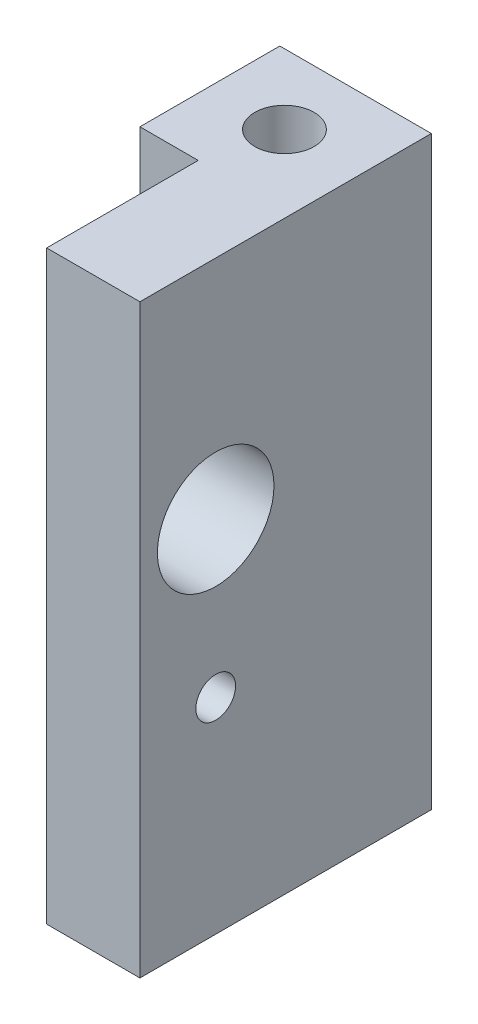
SolidWorks part; units mm, degrees
material "PET"
ref_plane "Front" through (0, 0, 0) normal (0, 0, 1) x (1, 0, 0)
ref_plane "Top" through (0, 0, 0) normal (0, 1, 0) x (1, 0, 0)
ref_plane "Right" through (0, 0, 0) normal (1, 0, 0) x (0, 0, -1)
sketch "Sketch1" plane through (0, 0, 0) normal (0, 1, 0) x (1, 0, 0)
  line L0 (0, 0) -> (-3.9688, 0)
  line L1 (-3.9688, 0) -> (-3.9688, 9.525)
  line L2 (-3.9688, 9.525) -> (6.35, 9.525)
  line L3 (6.35, 9.525) -> (6.35, -10.3187)
  line L4 (6.35, -10.3187) -> (0, -10.3187)
  line L5 (0, -10.3187) -> (0, 0)
  dimension "D2" = 9.525
  dimension "D3" = 19.8438
  dimension "D4" = 6.35
  dimension "D6" = 10.3187
extrude "Boss-Extrude1" add sketch "Sketch1" along normal blind 39.878
sketch "Sketch6" plane through (0, 39.878, 0) normal (0, 1, 0) x (1, 0, 0)
  line L16 (6.35, 9.525) -> (-3.9688, 9.525) construction
  line L17 (-3.9688, 9.525) -> (-3.9688, 0) construction
  point P0 (1.1112, 4.7625)
  dimension "D1" = 4.7625
  dimension "D2" = 5.08
hole_wizard "#10-32 Tapped Hole1" positions "Sketch6" profile "Sketch5" tap size "#10-32" standard "ANSI Inch" end condition up to next
sketch "Sketch5" plane through (1.1112, 39.878, -4.7625) normal (1, 0, 0) x (0, 0, 1)
  line L0 (0, 0) -> (0, 39.878)
  line L1 (0, 39.878) -> (2.0193, 39.878)
  line L2 (2.0193, 39.878) -> (2.0193, 0)
  line L5 (2.0193, 0) -> (0, 0)
  line L11 (0, -6.35) -> (0, 107.95) construction
  dimension "Thru Tap Drill Dia." = 4.0386
  dimension "Thru Tap Drill Depth" = 39.878
cosmetic thread "Hole Thread1" parameters "D2"=4.826
sketch "Sketch9" plane through (0, 0, 0) normal (-1, 0, 0) x (0, 0, 1)
  line L2 (0, 39.878) -> (0, 0) construction
  line L4 (10.3187, 39.878) -> (10.3187, 0) construction
  line L5 (0, 0) -> (10.3187, 0) construction
  line L6 (0, 13.9725) -> (5.1594, 13.9725) construction
  line L7 (5.1594, 13.9725) -> (10.3187, 13.9725) construction
  point P19 (5.1594, 13.9725)
  dimension "D2" = 13.9725
hole_wizard "#6-32 Tapped Hole1" positions "Sketch9" profile "Sketch8" tap size "#6-32" standard "ANSI Inch" end condition up to next
sketch "Sketch8" plane through (0, 13.9725, 5.1594) normal (0, 1, 0) x (0, 0, 1)
  line L0 (0, 0) -> (0, 6.35)
  line L1 (0, 6.35) -> (1.3525, 6.35)
  line L2 (1.3525, 6.35) -> (1.3525, 0)
  line L5 (1.3525, 0) -> (0, 0)
  line L11 (0, -6.35) -> (0, 107.95) construction
  dimension "Thru Tap Drill Dia." = 2.7051
  dimension "Thru Tap Drill Depth" = 6.35
cosmetic thread "Hole Thread3" parameters "D2"=3.5052
sketch "Sketch10" plane through (6.35, 0, 0) normal (1, 0, 0) x (0, 0, -1)
  circle A0 centre (-5.1594, 24.4725) radius 3.9687
  dimension "D1" = 7.9375
extrude "Cut-Extrude1" cut sketch "Sketch10" against normal up to next
mirror "Mirror1" [suppressed]
cosmetic thread "Hole Thread4" [suppressed] parameters "D2"=4.826
cosmetic thread "Hole Thread5" [suppressed] parameters "D2"=3.5052
delete or keep bodies "Body-Delete/Keep 1" [suppressed] type delete bodies bodies 113
